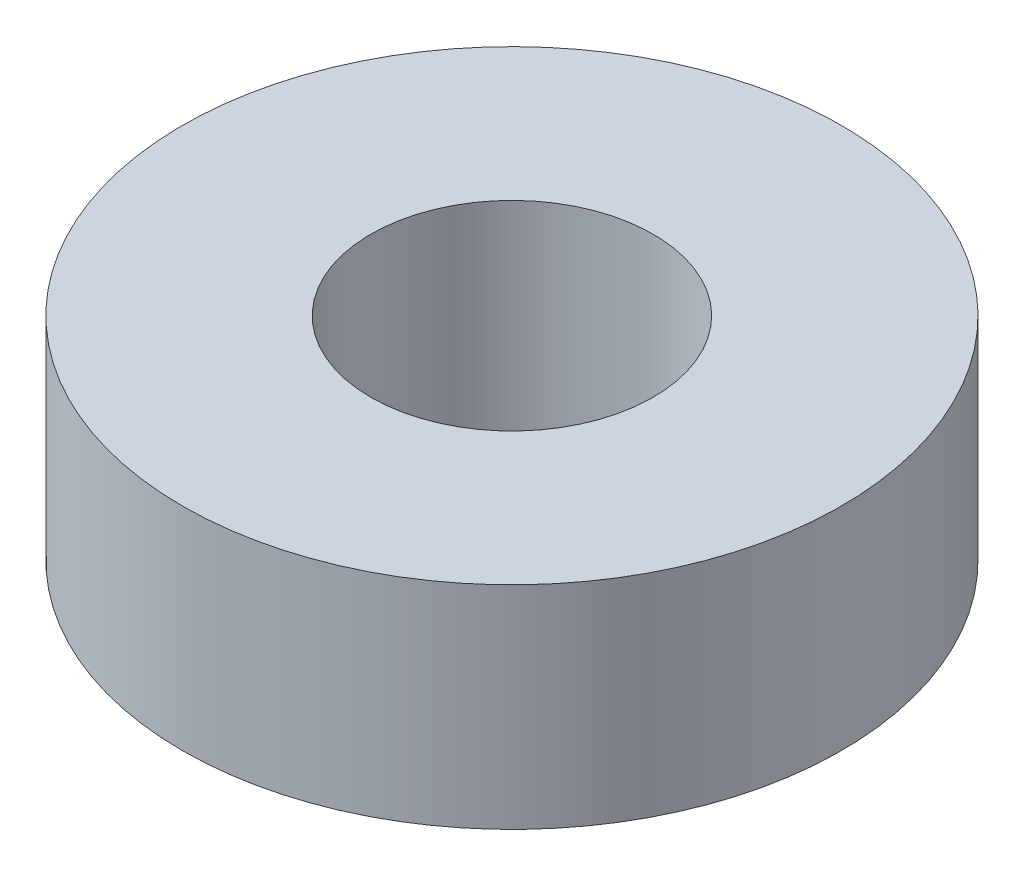
SolidWorks part; units mm, degrees
material "Cast Alloy Steel"
ref_plane "Front Plane" through (0, 0, 0) normal (0, 0, 1) x (1, 0, 0)
ref_plane "Top Plane" through (0, 0, 0) normal (0, 1, 0) x (1, 0, 0)
ref_plane "Right Plane" through (0, 0, 0) normal (1, 0, 0) x (0, 0, -1)
sketch "Sketch1" plane through (0, 0, 0) normal (0, 1, 0) x (1, 0, 0)
  circle A0 centre (0, 0) radius 4.7625
  circle A1 centre (0, 0) radius 11.1125
  dimension "D1" = 22.225
  dimension "D2" = 9.525
extrude "Boss-Extrude1" add sketch "Sketch1" along normal mid plane 7.1437
